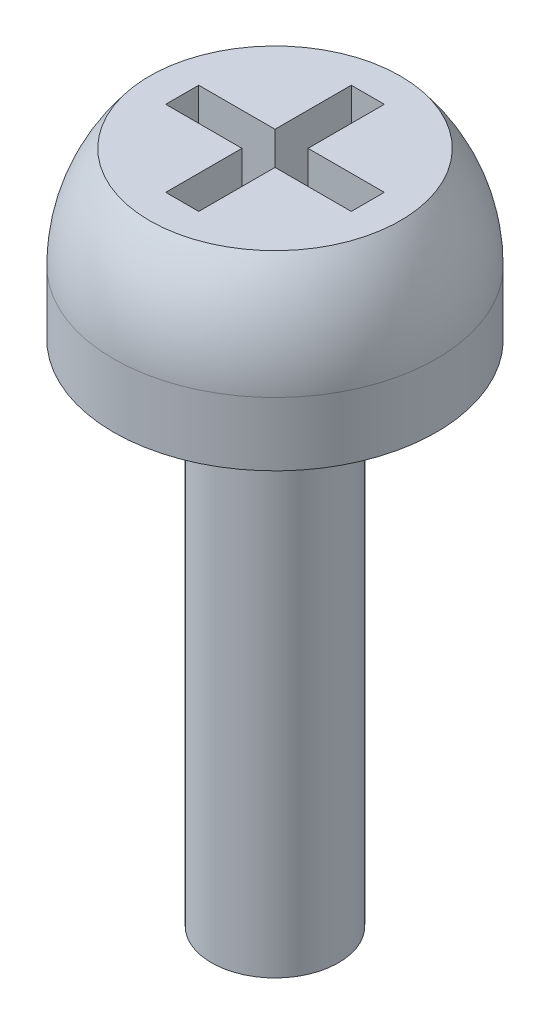
SolidWorks part; units mm, degrees
material "AISI 1020"
ref_plane "Front Plane" through (0, 0, 0) normal (0, 0, 1) x (1, 0, 0)
ref_plane "Top Plane" through (0, 0, 0) normal (0, 1, 0) x (1, 0, 0)
ref_plane "Right Plane" through (0, 0, 0) normal (1, 0, 0) x (0, 0, -1)
sketch "Sketch1" plane through (0, 0, 0) normal (0, 1, 0) x (1, 0, 0)
  circle A0 centre (0, 0) radius 1.27
  dimension "D1" = 2.54
extrude "Boss-Extrude1" add sketch "Sketch1" along normal blind 0.5
ref_plane "Plane1" through (0, 0.5, 0) normal (0, 1, 0) x (1, 0, 0)
sketch "Sketch2" plane through (0, 0.5, 0) normal (0, 1, 0) x (1, 0, 0)
  line L0 (0, 1.27) -> (0, -1.27)
  circle A0 centre (0, 0) radius 1.27 construction
  arc A1 (0, 1.27) -> (0, -1.27) centre (0, 0) ccw
revolve "Revolve1" add sketch "Sketch2" angle 180 about L0
ref_plane "Plane2" through (0, 1.3, 0) normal (0, -1, 0) x (-1, 0, 0)
sketch "Sketch4" plane through (0, 1.3, 0) normal (0, -1, 0) x (-1, 0, 0)
  circle A0 centre (0, 0) radius 2.5
  dimension "D1" = 5
extrude "Cut-Extrude2" cut sketch "Sketch4" against normal blind 1.016
sketch "Sketch5" plane through (0, 1.3, 0) normal (0, -1, 0) x (-1, 0, 0)
  line L0 (0, 0.9864) -> (0, -0.9864) construction
  line L1 (0.9864, 0) -> (-0.9864, 0) construction
  line L2 (0.13, 0.13) -> (0.13, 0.73)
  line L3 (0.13, -0.73) -> (-0.13, -0.73)
  line L4 (0.13, -0.73) -> (0.13, -0.13)
  line L5 (0.13, 0.73) -> (-0.13, 0.73)
  line L6 (-0.13, -0.73) -> (-0.13, -0.13)
  line L7 (-0.13, 0.13) -> (-0.13, 0.73)
  line L8 (-0.13, 0.13) -> (-0.73, 0.13)
  line L9 (0.73, 0.13) -> (0.13, 0.13)
  line L10 (0.73, 0.13) -> (0.73, -0.13)
  line L11 (0.73, -0.13) -> (0.13, -0.13)
  line L12 (-0.73, 0.13) -> (-0.73, -0.13)
  line L13 (-0.13, -0.13) -> (-0.73, -0.13)
  circle A0 centre (0, 0) radius 0.9864 construction
  point P7 (0, 0)
  point P12 (0, 0)
  dimension "D1" = 0.13
  dimension "D2" = 0.13
  dimension "D3" = 0.6
  dimension "D4" = 0.6
  dimension "D5" = 0.26
  dimension "D6" = 0.6
  dimension "D7" = 0.13
  dimension "D8" = 1.46
extrude "Cut-Extrude3" cut sketch "Sketch5" along normal blind 1.016
sketch "Sketch6" plane through (0, 0, 0) normal (0, -1, 0) x (1, 0, 0)
  circle A0 centre (0, 0) radius 0.5
  dimension "D1" = 1
extrude "Boss-Extrude2" add sketch "Sketch6" along normal blind 4
